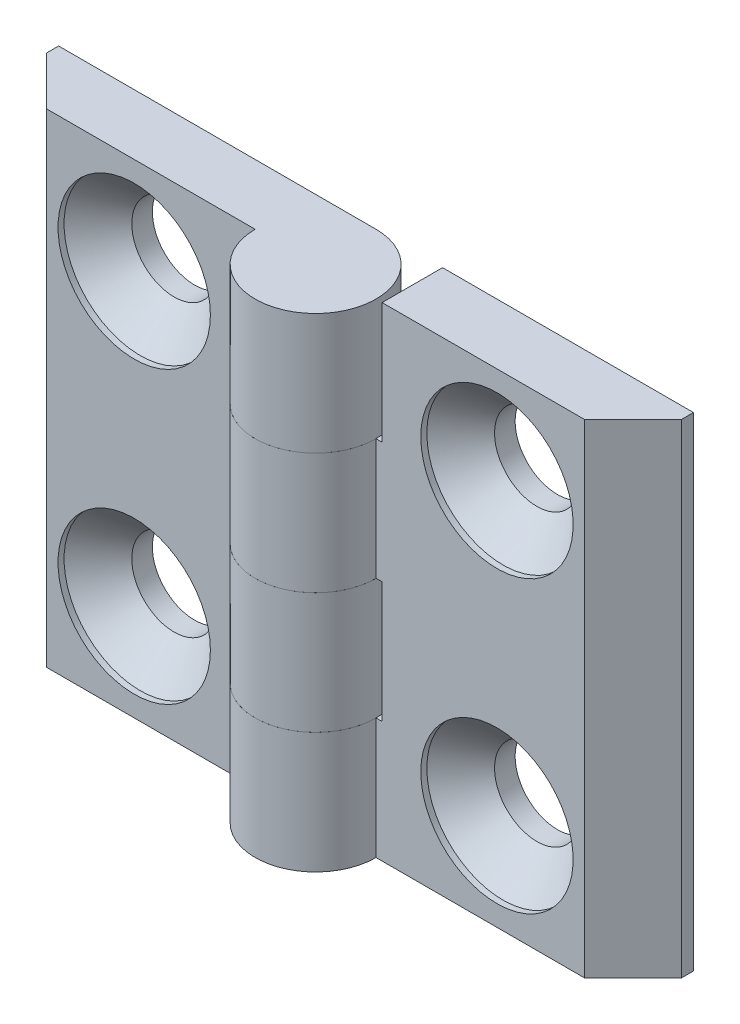
SolidWorks part; units mm, degrees
material "Алюминиевый сплав"
ref_plane "Спереди" through (0, 0, 0) normal (0, 0, 1) x (1, 0, 0)
ref_plane "Сверху" through (0, 0, 0) normal (0, 1, 0) x (1, 0, 0)
ref_plane "Справа" through (0, 0, 0) normal (1, 0, 0) x (0, 0, -1)
sketch "Эскиз1" plane through (0, 0, 0) normal (0, 1, 0) x (1, 0, 0)
  line L0 (0, 5) -> (-26.25, 5)
  line L1 (-26.25, 5) -> (-26.25, 4)
  line L2 (-26.25, 4) -> (-22.25, 0)
  line L3 (-22.25, 0) -> (-5, 0)
  line L4 (0, 0) -> (0, 10.5526) construction
  arc A0 (-5, 0) -> (0, 5) centre (0, 0) ccw
  dimension "D1" = 52.5
  dimension "D2" = 5
  dimension "D3" = 1
  dimension "D4" = 45
extrude "Бобышка-Вытянуть1" add sketch "Эскиз1" along normal mid plane 40
sketch "Эскиз3" plane through (0, 0, 0) normal (0, 0, 1) x (1, 0, 0)
  line L0 (5, -20) -> (5, 20) construction
  line L1 (-5.5, 10) -> (5, 10)
  line L2 (-5.5, 10) -> (-5.5, 0)
  line L3 (-5.5, 0) -> (5, 0)
  line L4 (5, 10) -> (5, 0)
  line L5 (5, 0) -> (5, -10) construction
  line L6 (5, -20) -> (-5.5, -20)
  line L7 (5, -20) -> (5, -10)
  line L8 (5, -10) -> (-5.5, -10)
  line L9 (-5.5, -20) -> (-5.5, -10)
  line L10 (5, 10) -> (5, 20) construction
  line L11 (-5, 20) -> (-5, -20) construction
  dimension "D1" = 0.5
extrude "Вырез-Вытянуть1" cut sketch "Эскиз3" against normal through all and the other way through all
hole_wizard "Зенковка для винта с полупотайной головкой M61" positions "Эскиз4" profile "Эскиз6" countersink size "M6" standard "ISO" end condition through all
sketch "Эскиз4" plane through (0, 0, 0) normal (0, 0, 1) x (1, 0, 0)
  line L0 (-15, 12) -> (-15, -12)
  line L2 (0, 0) -> (0, 18.9001) construction
  line L3 (5, 0) -> (-5, 0) construction
  point P0 (-15, 12)
  point P2 (-15, -12)
  point P9 (-15, 0)
  dimension "D1" = 24
  dimension "D2" = 30
sketch "Эскиз6" plane through (-15, 12, 0) normal (1, 0, 0) x (0, -1, 0)
  line L0 (0, 0) -> (0, 5)
  line L1 (0, 5) -> (3.5, 5)
  line L2 (3.5, 5) -> (3.5, 3.3)
  line L3 (3.5, 3.3) -> (6.3, 0.5)
  line L4 (6.3, 0.5) -> (6.3, 0)
  line L6 (6.3, 0) -> (0, 0)
  line L7 (-3.5, 3.3) -> (-6.3, 0.5) construction
  line L11 (0, -6.35) -> (0, 107.95) construction
  dimension "Диаметр сквозного отверстия" = 7
  dimension "Глубина сквозного отверстия" = 5
  dimension "Диаметр зенковки" = 12.6
  dimension "Угол зенковки" = 90
  dimension "Утопленность" = 0.5
sketch "Угол раскрытия" plane through (0, 0, 0) normal (0, 1, 0) x (1, 0, 0)
  line L0 (0, 0) -> (0, -10)
  line L7 (0, 5) -> (-26.25, 5) construction
  point P3 (-11.2006, -8.7746)
  point P8 (-7.4924, -9.3736)
  point P9 (0, 0)
  point P10 (-11.8016, -2.1731)
  dimension "D1" = 10
  dimension "D2" = 90
pattern_circular "Круговой массив1" count 2 over 360 about axis through (0, 0, 0) along (0, 0, 1) of bodies 106
